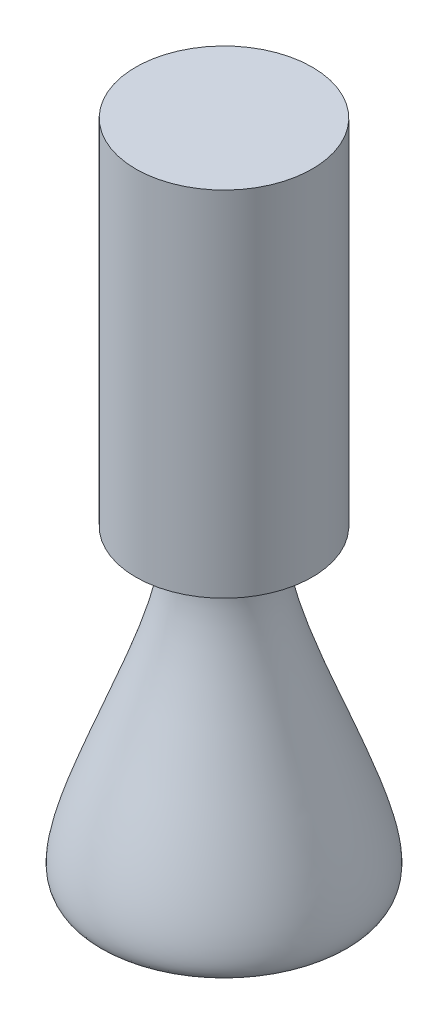
SolidWorks part; units mm, degrees
ref_plane "Front Plane" through (0, 0, 0) normal (0, 0, 1) x (1, 0, 0)
ref_plane "Top Plane" through (0, 0, 0) normal (0, 1, 0) x (1, 0, 0)
ref_plane "Right Plane" through (0, 0, 0) normal (1, 0, 0) x (0, 0, -1)
sketch "Sketch1" plane through (0, 0, 0) normal (0, 0, 1) x (1, 0, 0)
  line L0 (0, 0) -> (17, 0)
  line L1 (12.2351, 42.2158) -> (12.2351, 91.2158)
  line L2 (0, 0) -> (0, 111.9677) construction
  line L3 (12.2351, 91.2158) -> (0, 91.2158)
  line L4 (0, 91.2158) -> (0, 0)
  spline S0 degree 3 poles (17, 0) (21.0678, 5.5861) (-4.6446, 47.4477) (12.2351, 42.2158) knots 0 0 0 0 1 1 1 1
  dimension "D2" = 49
  dimension "D1" = 17
  dimension "D3" = 49
revolve "Revolve1" add sketch "Sketch1" angle 360 about L2
